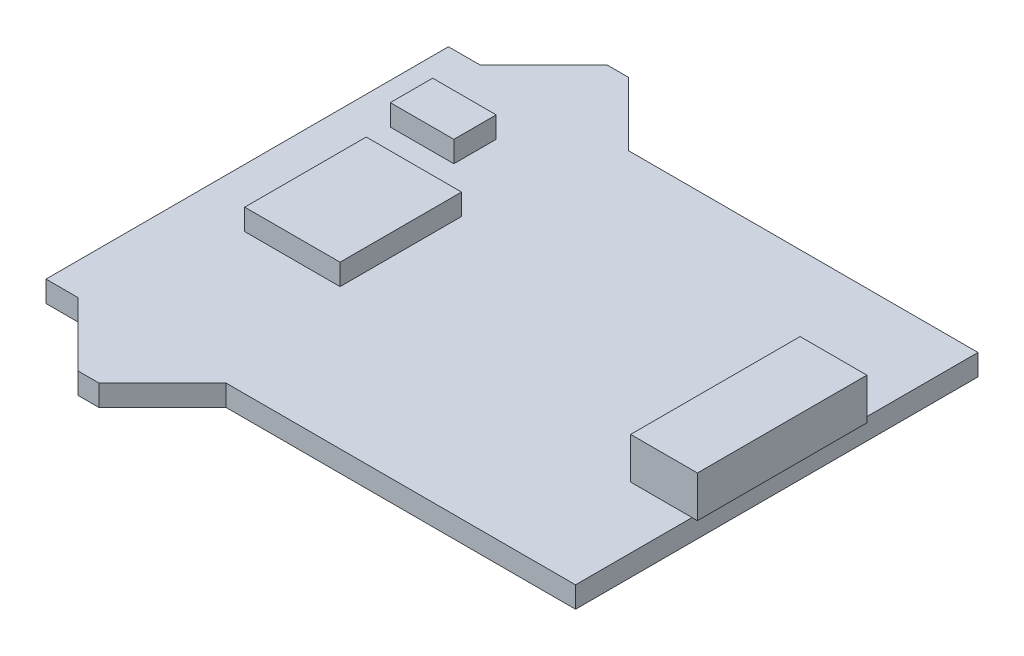
SolidWorks part; units mm, degrees
ref_plane "Front Plane" through (0, 0, 0) normal (0, 0, 1) x (1, 0, 0)
ref_plane "Top Plane" through (0, 0, 0) normal (0, 1, 0) x (1, 0, 0)
ref_plane "Right Plane" through (0, 0, 0) normal (1, 0, 0) x (0, 0, -1)
sketch "Sketch1" plane through (0, 0, 0) normal (0, 1, 0) x (1, 0, 0)
  line L0 (-3.5, 9.5) -> (-0.5, 12.5)
  line L1 (-5, -9.5) -> (5, -9.5) construction
  line L2 (-5, -9.5) -> (-5, 9.5) construction
  line L3 (-5, 9.5) -> (-3.5, 9.5)
  line L4 (5, -9.5) -> (5, 9.5) construction
  line L5 (-5, -9.5) -> (5, 9.5) construction
  line L6 (-5, 9.5) -> (5, -9.5) construction
  line L7 (-0.5, 12.5) -> (0.5, 12.5)
  line L8 (0.5, 12.5) -> (3.5, 9.5)
  line L9 (3.5, 9.5) -> (5, 9.5)
  line L10 (-5, 0) -> (5, 0) construction
  line L11 (3.5, -9.5) -> (5, -9.5)
  line L12 (5, 9.5) -> (20, 9.5)
  line L13 (5, 9.5) -> (5, -9.5) construction
  line L14 (5, -9.5) -> (20, -9.5)
  line L15 (20, 9.5) -> (20, -9.5)
  line L16 (0.5, -12.5) -> (3.5, -9.5)
  line L17 (-0.5, -12.5) -> (0.5, -12.5)
  line L18 (-5, -9.5) -> (-3.5, -9.5)
  line L19 (-3.5, -9.5) -> (-0.5, -12.5)
  line L20 (-5, 9.5) -> (-5, -9.5)
  point P0 (0, 0)
  point P8 (0, 12.5)
  dimension "D1" = 19
  dimension "D2" = 3
  dimension "D3" = 5
  dimension "D4" = 7
  dimension "D5" = 25
extrude "Boss-Extrude1" add sketch "Sketch1" against normal blind 1
sketch "Sketch2" plane through (0, 0, 0) normal (0, 1, 0) x (1, 0, 0)
  line L1 (-2.25, -2.8676) -> (2.25, -2.8676)
  line L2 (-2.25, -2.8676) -> (-2.25, 2.8676)
  line L3 (-2.25, 2.8676) -> (2.25, 2.8676)
  line L4 (2.25, -2.8676) -> (2.25, 2.8676)
  line L5 (-2.25, -2.8676) -> (2.25, 2.8676) construction
  line L6 (-2.25, 2.8676) -> (2.25, -2.8676) construction
  line L7 (-3.0875, 4.842) -> (-0.0875, 4.842)
  line L8 (-3.0875, 4.842) -> (-3.0875, 6.842)
  line L9 (-3.0875, 6.842) -> (-0.0875, 6.842)
  line L10 (-0.0875, 4.842) -> (-0.0875, 6.842)
  line L11 (-3.0875, 4.842) -> (-0.0875, 6.842) construction
  line L12 (-3.0875, 6.842) -> (-0.0875, 4.842) construction
  point P0 (0, 0)
  point P6 (-1.5875, 5.842)
  dimension "D1" = 5.7352
  dimension "D2" = 4.5
  dimension "D3" = 3
  dimension "D4" = 2
  dimension "D5" = 5.842
  dimension "D6" = 1.5875
extrude "Boss-Extrude2" add sketch "Sketch2" along normal blind 1
sketch "Sketch3" plane through (0, 0, 0) normal (0, 1, 0) x (1, 0, 0)
  line L5 (20, -9.5) -> (20, 9.5) construction
  line L6 (17.1, -4) -> (17.1, 4)
  line L8 (17.1, -4) -> (20.254, -4)
  line L9 (20.254, -4) -> (20.254, 4)
  line L10 (17.1, 4) -> (20.254, 4)
  point P4 (22.2637, -8.7022)
  point P5 (16.423, -6.6644)
  point P6 (16.3105, -5.7805)
  point P7 (20.866, 4.8291)
  point P8 (17.1, 0)
  point P12 (21.3269, 4.8956)
  point P13 (16.4089, -4.8956)
  dimension "D1" = 8
  dimension "D3" = 0.254
  dimension "D2" = 2.9
extrude "Boss-Extrude3" add sketch "Sketch3" along normal blind 1.95
sketch "Sketch4" plane through (0, 0, 0) normal (0, 1, 0) x (1, 0, 0)
  line L1 (17.8272, 3.99) -> (21.3134, 3.99)
  line L2 (17.8272, 3.99) -> (17.8272, -4.5386)
  line L3 (17.8272, -4.5386) -> (21.3134, -4.5386)
  line L4 (21.3134, 3.99) -> (21.3134, -4.5386)
extrude "Boss-Extrude4" [suppressed] add sketch "Sketch4" along normal blind 3
equation "\"width\"= 19mm"
equation "\"D1@Sketch1\"=\"width\""
equation "\"encoder_side_offse\"= 5mm"
equation "\"D3@Sketch1\"=\"encoder_side_offse\""
equation "\"nub_height\"= 3mm"
equation "\"D2@Sketch1\"=\"nub_height\""
equation "\"nub_width\"= 7mm"
equation "\"D4@Sketch1\"=\"nub_width\""
equation "\"pcb_length\"= 25mm"
equation "\"pcb_thickness\"= 1mm"
equation "\"D1@Boss-Extrude1\"=\"pcb_thickness\""
equation "\"encoder_width\"= 6mm"
equation "\"encoder_length\"= 4.5mm"
equation "\"D2@Sketch2\"=\"encoder_length\""
equation "\"plugin_side_offset\"= 1.5mm"
equation "\"connector_length\" = 2.9mm"
equation "\"D5@Sketch1\"=\"pcb_length\""
equation "\"connector_height\" = 1.95mm"
equation "\"connector_width\"= 8mm"
equation "\"D2@Sketch3\"=\"connector_length\""
equation "\"D1@Sketch3\"=\"connector_width\""
equation "\"D1@Boss-Extrude3\"=\"connector_height\""
